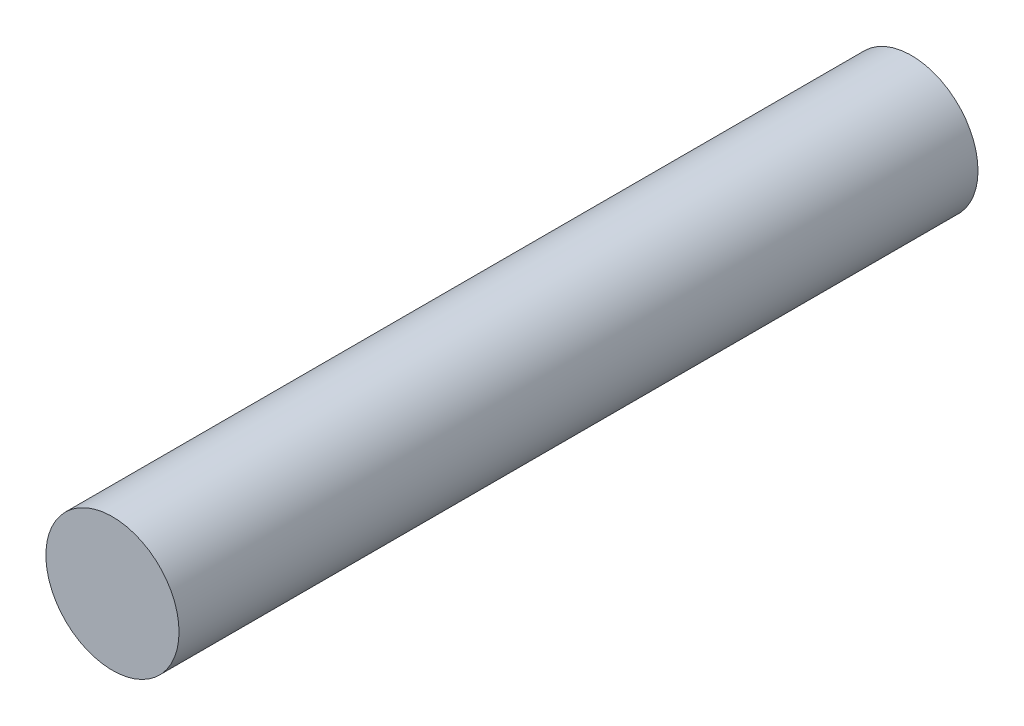
SolidWorks part; units mm, degrees
material "AISI 304"
ref_plane "Front Plane" through (0, 0, 0) normal (0, 0, 1) x (1, 0, 0)
ref_plane "Top Plane" through (0, 0, 0) normal (0, 1, 0) x (1, 0, 0)
ref_plane "Right Plane" through (0, 0, 0) normal (1, 0, 0) x (0, 0, -1)
sketch "Sketch1" plane through (0, 0, 0) normal (0, 0, 1) x (1, 0, 0)
  circle A0 centre (0, 0) radius 1.25
  dimension "D1" = 2.5
extrude "Boss-Extrude1" add sketch "Sketch1" along normal blind 15
